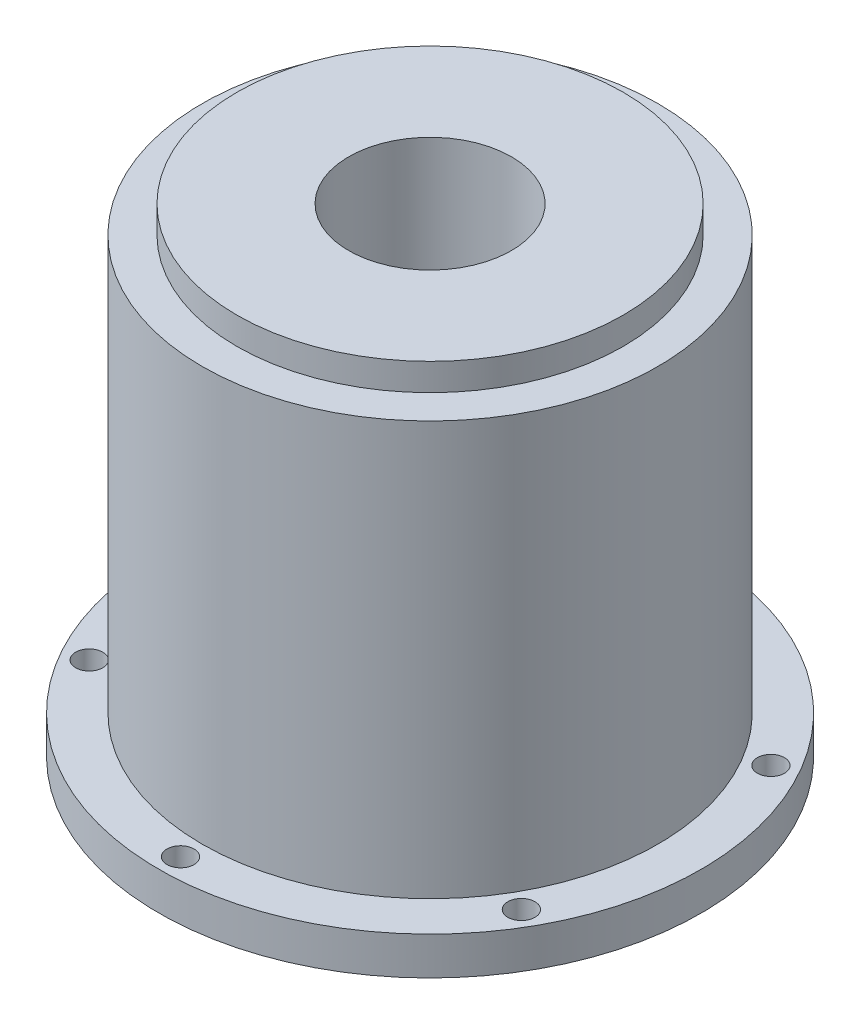
SolidWorks part; units mm, degrees
ref_plane "Front Plane" through (0, 0, 0) normal (0, 0, 1) x (1, 0, 0)
ref_plane "Top Plane" through (0, 0, 0) normal (0, 1, 0) x (1, 0, 0)
ref_plane "Right Plane" through (0, 0, 0) normal (1, 0, 0) x (0, 0, -1)
sketch "Sketch1" plane through (0, 0, 0) normal (0, 0, 1) x (1, 0, 0)
  line L0 (0, 0) -> (0, 74.2711) construction
  line L1 (7.5, 57.8219) -> (7.5, 7.2219)
  line L2 (7.5, 57.8219) -> (17.8018, 57.8219)
  line L3 (17.8018, 57.8219) -> (17.8018, 55.3219)
  line L4 (17.8018, 55.3219) -> (21, 55.3219)
  line L7 (21, 55.3219) -> (21, 17.1864)
  line L8 (21, 17.1864) -> (25, 17.1864)
  line L9 (25, 17.1864) -> (25, 13.6864)
  line L10 (25, 13.6864) -> (15, 13.6864)
  line L11 (15, 13.6864) -> (15, 7.2219)
  line L12 (15, 7.2219) -> (7.5, 7.2219)
  line L21 (8.7, 53.5219) -> (19.6, 53.5219)
  line L22 (19.6, 53.5219) -> (19.6, 15.9319)
  line L23 (19.6, 15.9319) -> (13.1138, 15.9319)
  line L24 (13.1138, 15.9319) -> (13.1138, 12.5169)
  line L25 (13.1138, 12.5169) -> (8.7, 12.5169)
  line L26 (8.7, 12.5169) -> (8.7, 53.5219)
  dimension "D1" = 15
  dimension "D2" = 50
  dimension "D3" = 2.5
  dimension "D4" = 50.6
  dimension "D5" = 30
  dimension "D6" = 4
  dimension "D7" = 3.5
  dimension "D8" = 1.2
  dimension "D9" = 1.4
  dimension "D10" = 4.3
revolve "Revolve1" add sketch "Sketch1" angle 360 about L0
sketch "Sketch2" plane through (0, 17.1864, 0) normal (0, 1, 0) x (1, 0, 0)
  circle A0 centre (0, 0) radius 23 construction
  circle A1 centre (0, 23) radius 1.25
  circle A2 centre (19.9186, 11.5) radius 1.25
  circle A3 centre (19.9186, -11.5) radius 1.25
  circle A4 centre (0, -23) radius 1.25
  circle A5 centre (-19.9186, -11.5) radius 1.25
  circle A6 centre (-19.9186, 11.5) radius 1.25
  point P18 (0, 0)
  dimension "D1" = 46
  dimension "D2" = 2.5
  dimension "D3" = 6
extrude "Cut-Extrude1" cut sketch "Sketch2" against normal blind 10
sketch "Sketch4" plane through (0, 12.5169, 0) normal (0, 1, 0) x (1, 0, 0)
  circle A0 centre (0, 0) radius 11 construction
  circle A1 centre (0, 11) radius 1.25
  circle A2 centre (9.5263, 5.5) radius 1.25
  circle A3 centre (9.5263, -5.5) radius 1.25
  circle A4 centre (0, -11) radius 1.25
  circle A5 centre (-9.5263, -5.5) radius 1.25
  circle A6 centre (-9.5263, 5.5) radius 1.25
  point P17 (0, 0)
  dimension "D1" = 22
  dimension "D2" = 2.5
  dimension "D3" = 6
extrude "Cut-Extrude2" cut sketch "Sketch4" against normal blind 10
